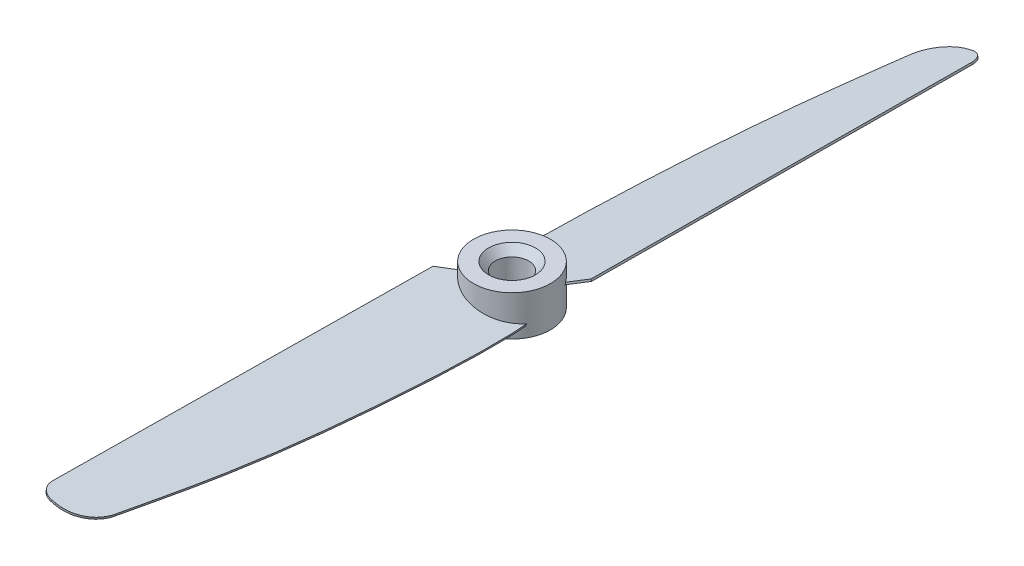
SolidWorks part; units mm, degrees
ref_plane "Front Plane" through (0, 0, 0) normal (0, 0, 1) x (1, 0, 0)
ref_plane "Top Plane" through (0, 0, 0) normal (0, 1, 0) x (1, 0, 0)
ref_plane "Right Plane" through (0, 0, 0) normal (1, 0, 0) x (0, 0, -1)
sketch "Sketch1" plane through (0, 0, 0) normal (0, 1, 0) x (1, 0, 0)
  circle A0 centre (0, 0) radius 5.75
  dimension "D1" = 11.5
extrude "Boss-Extrude1" add sketch "Sketch1" along normal mid plane 6
sketch "Sketch2" plane through (0, 0, 0) normal (0, 0, 1) x (1, 0, 0)
  line L0 (-5.75, 1.3275) -> (5.75, -1.3275) construction
  line L1 (-5.75, 3) -> (-5.75, -3) construction
  line L2 (5.75, -3) -> (5.75, 3) construction
  line L3 (-5.75, -3) -> (5.75, -3) construction
  dimension "D1" = 13
ref_plane "Plane1" through (0, 0, 0) normal (-0.225, -0.9744, 0) x (0.9744, -0.225, 0)
sketch "Sketch3" plane through (0, 0, 0) normal (-0.225, -0.9744, 0) x (0.9744, -0.225, 0)
  line L0 (-4.3186, 2.6076) -> (-6.9062, 5.0835)
  line L1 (-6.9062, 5.0835) -> (-7.4531, 61.4806)
  line L2 (-5.4532, 63.5) -> (-4.8649, 63.5)
  line L3 (5.1131, 2.5494) -> (-4.3186, 2.6076)
  arc A0 (0.0805, 59.2367) -> (-4.8649, 63.5) centre (-4.8649, 58.5) ccw
  arc A1 (-7.4531, 61.4806) -> (-5.4532, 63.5) centre (-5.4532, 61.5) cw
  spline S0 degree 3 poles (5.1131, 2.5494) (5.7356, 8.029) (4.3463, 38.9767) (0.3831, 57.2051) (0.0805, 59.2367) knots 0 0 0 0 0.5525 0.930981 0.930981 0.930981 0.930981
  dimension "D2" = 5
  dimension "D3" = 2
  dimension "D1" = 63.5
extrude "Boss-Extrude2" add sketch "Sketch3" along normal blind 0.3
pattern_circular "CirPattern1" count 2 over 360 about axis through (0, -3, 0) along (0, 1, 0) of "Boss-Extrude2"
sketch "Sketch4" plane through (0, -3, 0) normal (0, -1, 0) x (1, 0, 0)
  circle A0 centre (0, 0) radius 2.5
  dimension "D1" = 5
extrude "Cut-Extrude1" cut sketch "Sketch4" against normal blind 16.3
chamfer "Chamfer1" distance 1 angle 50 2 edges at (0, -3, -2.5) (0, 3, 2.5)
